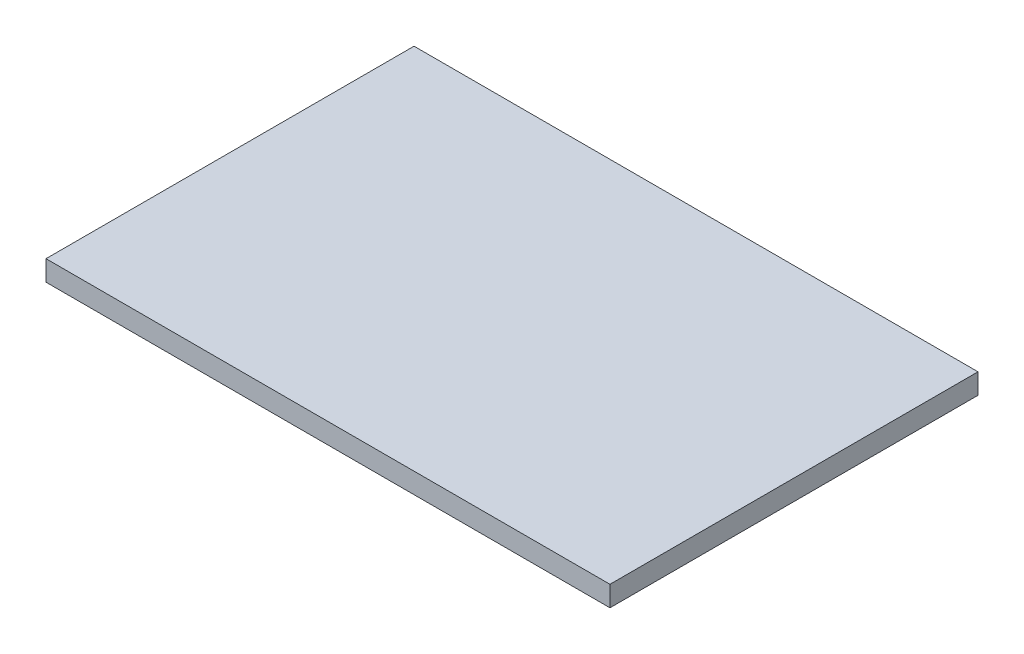
SolidWorks part; units mm, degrees
ref_plane "Спереди" through (0, 0, 0) normal (0, 0, 1) x (1, 0, 0)
ref_plane "Сверху" through (0, 0, 0) normal (0, 1, 0) x (1, 0, 0)
ref_plane "Справа" through (0, 0, 0) normal (1, 0, 0) x (0, 0, -1)
sketch "Эскиз1" plane through (0, 0, 0) normal (0, 1, 0) x (1, 0, 0)
  line L1 (249, -162.5) -> (-249, -162.5)
  line L2 (249, -162.5) -> (249, 162.5)
  line L3 (249, 162.5) -> (-249, 162.5)
  line L4 (-249, -162.5) -> (-249, 162.5)
  line L5 (249, -162.5) -> (-249, 162.5) construction
  line L6 (249, 162.5) -> (-249, -162.5) construction
  point P0 (0, 0)
  dimension "D1" = 325
  dimension "D2" = 498
extrude "Бобышка-Вытянуть1" add sketch "Эскиз1" along normal blind 18
